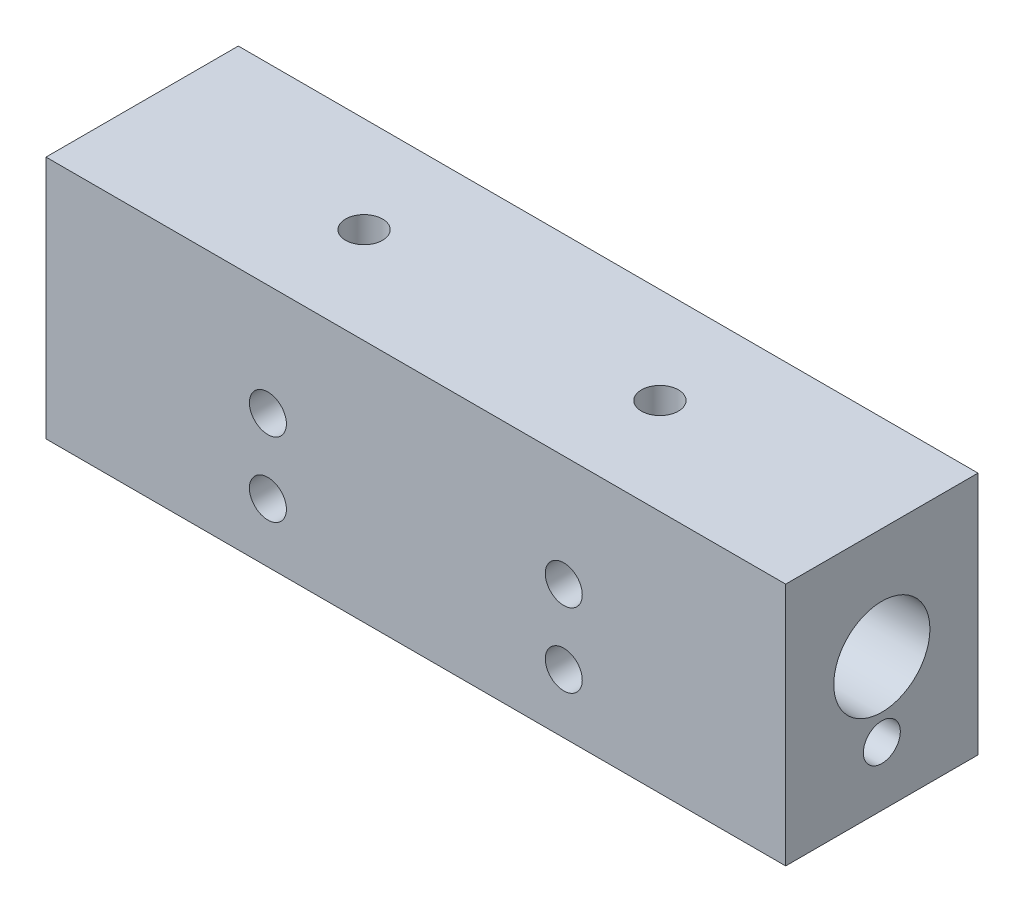
SolidWorks part; units mm, degrees
ref_plane "Front Plane" through (0, 0, 0) normal (0, 0, 1) x (1, 0, 0)
ref_plane "Top Plane" through (0, 0, 0) normal (0, 1, 0) x (1, 0, 0)
ref_plane "Right Plane" through (0, 0, 0) normal (1, 0, 0) x (0, 0, -1)
sketch "Sketch1" plane through (0, 0, 0) normal (0, 0, 1) x (1, 0, 0)
  line L1 (-25, -8.25) -> (25, -8.25)
  line L2 (-25, -8.25) -> (-25, 8.25)
  line L3 (-25, 8.25) -> (25, 8.25)
  line L4 (25, -8.25) -> (25, 8.25)
  line L5 (-25, -8.25) -> (25, 8.25) construction
  line L6 (-25, 8.25) -> (25, -8.25) construction
  point P0 (0, 0)
  dimension "D1" = 50
  dimension "D2" = 16.5
extrude "Boss-Extrude1" add sketch "Sketch1" along normal mid plane 13
hole_wizard "M3x0.5 Tapped Hole1" positions "Sketch3" profile "Sketch2" tap size "M3x0.5" standard "ANSI Metric"
sketch "Sketch3" plane through (0, 8.25, 0) normal (0, 1, 0) x (1, 0, 0)
  line L0 (25, -6.5) -> (25, 6.5) construction
  line L1 (25, 6.5) -> (25, -6.5) construction
  point P0 (10, 0)
  point P9 (25, 0)
  dimension "D1" = 15
sketch "Sketch2" plane through (10, 8.25, 0) normal (1, 0, 0) x (0, 0, 1)
  line L0 (0, 0) -> (0, 7.5)
  line L1 (0, 7.5) -> (1.25, 6.7489)
  line L2 (1.25, 6.7489) -> (1.25, 0)
  line L5 (1.25, 0) -> (0, 0)
  line L10 (0, 7.5) -> (-1.25, 6.7489) construction
  line L11 (0, -6.35) -> (0, 107.95) construction
  dimension "Tap Drill Dia." = 2.5
  dimension "Tap Drill Depth" = 7.5
  dimension "Drill Angle" = 118
cosmetic thread "Hole Thread1" parameters "D1"=6, "D2"=3
pattern_linear "LPattern1" count 2 spacing 20 along (-1, 0, 0) of "M3x0.5 Tapped Hole1"
cosmetic thread "Hole Thread2" parameters "D1"=6, "D2"=3
sketch "Sketch4" plane through (25, 0, 0) normal (1, 0, 0) x (0, 0, -1)
  line L0 (-6.5, 8.25) -> (6.5, 8.25) construction
  circle A0 centre (0, 0.75) radius 3.25
  point P4 (0, 0)
  point P5 (0, 0)
  dimension "D2" = 6.5
  dimension "D1" = 7.5
extrude "Cut-Extrude1" cut sketch "Sketch4" against normal through all
hole_wizard "M3x0.5 Tapped Hole2" positions "Sketch5" profile "Sketch6" tap size "M3x0.5" standard "ANSI Metric" end condition through all
sketch "Sketch5" plane through (25, 0, 0) normal (1, 0, 0) x (0, 0, -1)
  circle A0 centre (0, 0.75) radius 3.25 construction
  point P0 (0, -4.25)
  dimension "D1" = 5
cosmetic thread "Hole Thread3" parameters "D2"=3
sketch "Sketch6" plane through (25, -4.25, 0) normal (0, 1, 0) x (0, 0, -1)
  line L0 (0, 0) -> (0, 50)
  line L1 (0, 50) -> (1.25, 50)
  line L2 (1.25, 50) -> (1.25, 0)
  line L5 (1.25, 0) -> (0, 0)
  line L11 (0, -6.35) -> (0, 107.95) construction
  dimension "Thru Tap Drill Dia." = 2.5
  dimension "Thru Tap Drill Depth" = 50
hole_wizard "M3x0.5 Tapped Hole3" positions "Sketch8" profile "Sketch7" tap size "M3x0.5" standard "ANSI Metric"
sketch "Sketch8" plane through (0, 0, 6.5) normal (0, 0, 1) x (1, 0, 0)
  line L0 (25, 8.25) -> (-25, 8.25) construction
  line L1 (-25, 8.25) -> (-25, -8.25) construction
  point P0 (-10, 0.75)
  dimension "D1" = 7.5
  dimension "D2" = 15
sketch "Sketch7" plane through (-10, 0.75, 6.5) normal (1, 0, 0) x (0, -1, 0)
  line L0 (0, 0) -> (0, 7.5)
  line L1 (0, 7.5) -> (1.25, 6.7489)
  line L2 (1.25, 6.7489) -> (1.25, 0)
  line L5 (1.25, 0) -> (0, 0)
  line L10 (0, 7.5) -> (-1.25, 6.7489) construction
  line L11 (0, -6.35) -> (0, 107.95) construction
  dimension "Tap Drill Dia." = 2.5
  dimension "Tap Drill Depth" = 7.5
  dimension "Drill Angle" = 118
cosmetic thread "Hole Thread4" parameters "D1"=6, "D2"=3
pattern_linear "LPattern2" count 2 spacing 20 along (1, 0, 0) count 2 spacing 5 along (0, -1, 0) of "M3x0.5 Tapped Hole3"
cosmetic thread "Hole Thread5" parameters "D1"=6, "D2"=3
cosmetic thread "Hole Thread6" parameters "D1"=6, "D2"=3
cosmetic thread "Hole Thread7" parameters "D1"=6, "D2"=3
sketch "Sketch9" plane through (0, -8.25, 0) normal (0, -1, 0) x (1, 0, 0)
  line L0 (-25, 6.5) -> (25, 6.5) construction
  line L1 (-8.5, 4.5) -> (8.5, 4.5)
  line L2 (-8.5, 4.5) -> (-8.5, 3.5)
  line L3 (-8.5, 3.5) -> (8.5, 3.5)
  line L4 (8.5, 4.5) -> (8.5, 3.5)
  line L5 (-25, 6.5) -> (-25, -6.5) construction
  dimension "D1" = 17
  dimension "D2" = 1
  dimension "D3" = 2
  dimension "D4" = 16.5
extrude "Boss-Extrude2" add sketch "Sketch9" along normal blind 2
